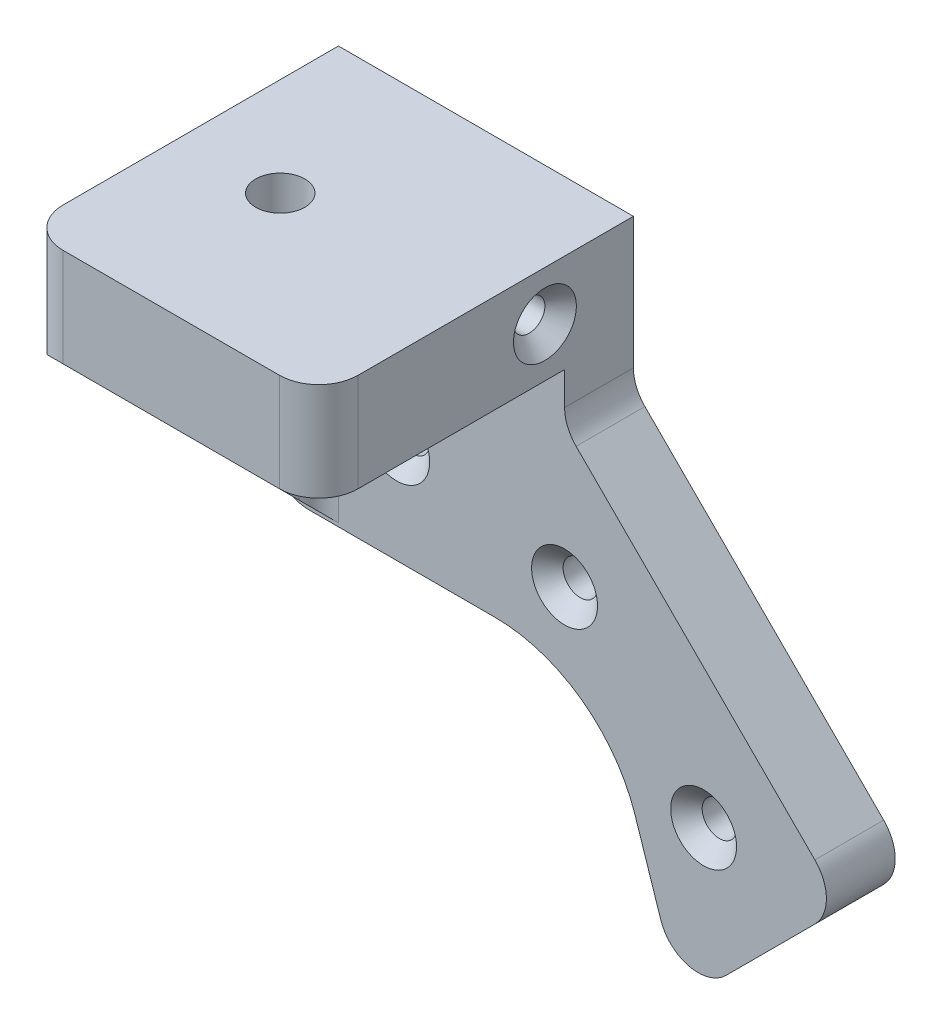
SolidWorks part; units mm, degrees
ref_plane "Front Plane" through (0, 0, 0) normal (0, 0, 1) x (1, 0, 0)
ref_plane "Top Plane" through (0, 0, 0) normal (0, 1, 0) x (1, 0, 0)
ref_plane "Right Plane" through (0, 0, 0) normal (1, 0, 0) x (0, 0, -1)
sketch "Sketch1" plane through (0, 0, 0) normal (0, 0, 1) x (1, 0, 0)
  line L0 (15, 27.5) -> (15, 12.5)
  line L5 (-15, 27.5) -> (15, 27.5)
  line L6 (-15, 27.5) -> (-15, -27.5)
  line L7 (-15, -27.5) -> (15, -27.5)
  line L9 (15, 12.5) -> (43.2843, -15.7843)
  line L10 (-15, -27.5) -> (15, 27.5) construction
  line L11 (43.2843, -15.7843) -> (23.2843, -35.7843)
  line L12 (23.2843, -35.7843) -> (15, -27.5)
  point P0 (0, 0)
  dimension "D1" = 45
  dimension "D2" = 55
  dimension "D3" = 30
  dimension "D4" = 40
  dimension "D5" = 15
extrude "Boss-Extrude1" add sketch "Sketch1" along normal blind 5 and the other way blind 2
sketch "Sketch3" plane through (0, 0, 5) normal (0, 0, 1) x (1, 0, 0)
  line L0 (15, 12.5) -> (15, 27.5) construction
  line L1 (-15, 27.5) -> (15, 27.5)
  line L2 (-15, 27.5) -> (-15, 17.5)
  line L3 (-15, 17.5) -> (15, 17.5)
  line L4 (15, 27.5) -> (15, 17.5)
  dimension "D1" = 10
extrude "Boss-Extrude2" add sketch "Sketch3" along normal blind 25
sketch "Sketch4" plane through (0, 27.5, 0) normal (0, 1, 0) x (1, 0, 0)
  line L0 (-15, -30) -> (-15, 2) construction
  line L1 (15, -30) -> (-15, -30) construction
  line L2 (15, -30) -> (15, -5) construction
  line L3 (15, -5) -> (-15, -5) construction
  line L4 (-15, -30) -> (-15, -5) construction
  line L5 (15, -30) -> (15, 2) construction
  line L6 (-15, 2) -> (15, 2) construction
  line L7 (-15, 2) -> (-15, 7) construction
  line L8 (-15, 7) -> (15, 7) construction
  line L9 (15, 2) -> (15, 7) construction
  line L10 (15, -20.575) -> (-15, -20.575) construction
  circle A0 centre (-5, -13.9175) radius 2.5
  circle A1 centre (-5, -13.9175) radius 6.6575 construction
  circle A2 centre (-5, -14.15) radius 6.425 construction
  dimension "D3" = 13.315
  dimension "D4" = 5
  dimension "D7" = 21.15
  dimension "D8" = 12.85
  dimension "D1" = 25
  dimension "D2" = 5
  dimension "D6" = 20
extrude "Cut-Extrude1" cut sketch "Sketch4" against normal through all
sketch "Sketch6" plane through (-15, 0, 0) normal (-1, 0, 0) x (0, 0, 1)
  line L0 (30, 17.5) -> (5, -7.5)
  line L1 (5, 17.5) -> (5, -27.5) construction
  dimension "D1" = 45
rib "Rib1" sketch "Sketch6" sketch "Sketch6" thickness 5 extrusion direction parallel to sketch draft on no parameters "D1"=5
sketch "Sketch7" plane through (0, 0, 5) normal (0, 0, 1) x (1, 0, 0)
  line L0 (22.1747, -18.1589) -> (26.8198, -32.2487)
  line L1 (-15, -7.8553) -> (7.9289, -7.8553)
  line L2 (-15, -7.8553) -> (-15, -27.5)
  line L3 (-15, -7.5) -> (-15, -27.5) construction
  line L4 (-15, -27.5) -> (15, -27.5) construction
  line L5 (15, 27.5) -> (-15, 27.5) construction
  line L6 (23.2843, -35.7843) -> (43.2843, -15.7843) construction
  line L7 (-15, -27.5) -> (23.2843, -35.7843)
  line L8 (23.2843, -35.7843) -> (26.8198, -32.2487)
  arc A0 (22.1747, -18.1589) -> (7.9289, -7.8553) centre (7.9289, -22.8553) ccw
  circle A1 centre (7.9289, -22.8553) radius 14 construction
  dimension "D1" = 1
  dimension "D2" = 5
extrude "Cut-Extrude2" cut sketch "Sketch7" against normal up to vertex (7 mm away)
sketch "Sketch8" plane through (0, 17.5, 0) normal (0, -1, 0) x (-1, 0, 0)
  line L1 (0.2657, -13.9175) -> (2.6329, -18.0175)
  line L2 (2.6329, -18.0175) -> (7.3671, -18.0175)
  line L3 (7.3671, -18.0175) -> (9.7343, -13.9175)
  line L4 (9.7343, -13.9175) -> (7.3671, -9.8175)
  line L5 (7.3671, -9.8175) -> (2.6329, -9.8175)
  line L6 (2.6329, -9.8175) -> (0.2657, -13.9175)
  circle A0 centre (5, -13.9175) radius 4.1 construction
  dimension "D1" = 8.2
extrude "Cut-Extrude3" cut sketch "Sketch8" against normal blind 5
fillet "Fillet1" radius 4 2 edges at (-15, 22.5, 30) (15, 22.5, 30)
sketch "Sketch9" plane through (0, 0, 5) normal (0, 0, 1) x (1, 0, 0)
  line L0 (15, -1.6421) -> (22.0711, 5.4289) construction
  line L1 (43.2843, -15.7843) -> (15, 12.5) construction
  line L2 (29.1421, -15.7843) -> (36.2132, -8.7132) construction
  line L3 (26.8198, -32.2487) -> (43.2843, -15.7843) construction
  line L4 (15, 12.5) -> (-5.3553, -7.8553) construction
  line L5 (7.9289, -7.8553) -> (-15, -7.8553) construction
  line L6 (15, 12.5) -> (-15, 12.5) construction
  line L7 (-15, 13.5) -> (-15, -7.5) construction
  circle A0 centre (15, -1.6421) radius 1.75
  circle A1 centre (29.1421, -15.7843) radius 1.75
  circle A2 centre (-2.0711, 2.5) radius 1.75
  dimension "D1" = 3.5
  dimension "D5" = 5
  dimension "D2" = 10
  dimension "D3" = 10
  dimension "D4" = 20
  dimension "D6" = 10
extrude "Cut-Extrude4" cut sketch "Sketch9" against normal through all
chamfer "Chamfer1" distance 1.6 angle 45 3 edges at (30.8921, -15.7843, 5) (16.75, -1.6421, 5) (-0.3211, 2.5, 5)
fillet "Fillet2" radius 4 4 edges at (15, 12.5, 1.5) (43.2843, -15.7843, 1.5) (26.8198, -32.2487, 1.5) (-15, -7.8553, 1.5)
sketch "Sketch10" plane through (15, 0, 0) normal (1, 0, 0) x (0, 0, -1)
  line L0 (-7, 17.5) -> (-7, 27.5) construction
  line L1 (-26, 17.5) -> (-5, 17.5) construction
  line L2 (-26, 27.5) -> (2, 27.5) construction
  line L3 (2, 14.1569) -> (2, 27.5) construction
  circle A0 centre (-7, 22.5) radius 1.6
  dimension "D1" = 3.2
  dimension "D2" = 9
extrude "Cut-Extrude5" cut sketch "Sketch10" against normal through all
sketch "Sketch11" plane through (-15, 0, 0) normal (-1, 0, 0) x (0, 0, 1)
  line L1 (8.5877, 19.75) -> (10.1754, 22.5)
  line L2 (10.1754, 22.5) -> (8.5877, 25.25)
  line L3 (8.5877, 25.25) -> (5.4123, 25.25)
  line L4 (5.4123, 25.25) -> (3.8246, 22.5)
  line L5 (3.8246, 22.5) -> (5.4123, 19.75)
  line L6 (5.4123, 19.75) -> (8.5877, 19.75)
  circle A0 centre (7, 22.5) radius 2.75 construction
  dimension "D1" = 5.5
extrude "Cut-Extrude6" cut sketch "Sketch11" against normal blind 4
chamfer "Chamfer2" distance 1.6 angle 45 1 edges at (15, 24.1, 7)
fillet "Fillet3" radius 2 1 edges at (-10, 5, 5)
